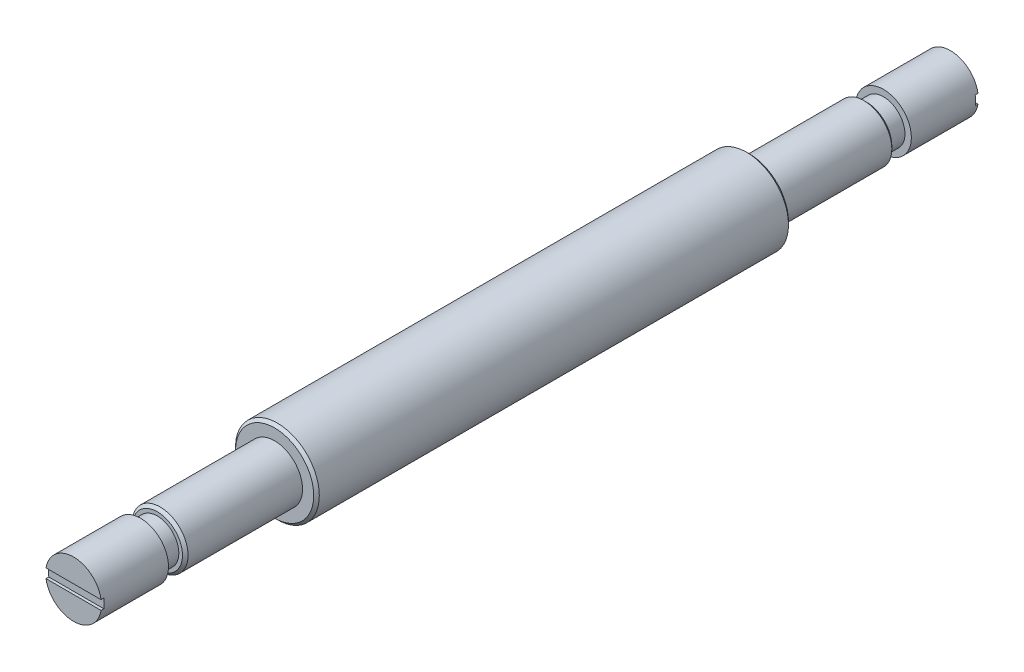
SolidWorks part; units mm, degrees
material "1.4301 (X5CrNi18-10)"
ref_plane "Plan de face" through (0, 0, 0) normal (0, 0, 1) x (1, 0, 0)
ref_plane "Plan de dessus" through (0, 0, 0) normal (0, 1, 0) x (1, 0, 0)
ref_plane "Plan de droite" through (0, 0, 0) normal (1, 0, 0) x (0, 0, -1)
sketch "Esquisse2" plane through (0, 0, 0) normal (1, 0, 0) x (0, 0, -1)
  line L0 (-66.5, 0) -> (-78.5, 0)
  line L1 (-42.5, 0) -> (42.5, 0)
  line L2 (0, 0) -> (0, 7.5)
  line L3 (-42.5, 7.5) -> (42.5, 7.5)
  line L4 (42.5, 0) -> (42.5, 7.5)
  line L5 (42.5, 0) -> (63.5, 0)
  line L6 (42.5, 0) -> (42.5, 5)
  line L7 (42.5, 5) -> (63.5, 5)
  line L8 (63.5, 0) -> (63.5, 5)
  line L9 (63.5, 0) -> (66.5, 0)
  line L10 (63.5, 0) -> (63.5, 3.85)
  line L11 (63.5, 3.85) -> (66.5, 3.85)
  line L12 (66.5, 0) -> (66.5, 3.85)
  line L13 (66.5, 0) -> (78.5, 0)
  line L14 (66.5, 0) -> (66.5, 5)
  line L15 (66.5, 5) -> (78.5, 5)
  line L16 (78.5, 0) -> (78.5, 5)
  line L17 (-78.5, 0) -> (-78.5, 5)
  line L18 (-66.5, 0) -> (-66.5, 5)
  line L19 (-63.5, 0) -> (-63.5, 5)
  line L20 (-66.5, 5) -> (-78.5, 5)
  line L21 (-66.5, 0) -> (-66.5, 3.85)
  line L22 (-63.5, 0) -> (-66.5, 0)
  line L23 (-63.5, 3.85) -> (-66.5, 3.85)
  line L24 (-42.5, 0) -> (-63.5, 0)
  line L25 (-42.5, 5) -> (-63.5, 5)
  line L26 (-42.5, 0) -> (-42.5, 7.5)
  dimension "D1" = 42.5
  dimension "D2" = 7.5
  dimension "D3" = 21
  dimension "D4" = 5
  dimension "D5" = 3
  dimension "D6" = 12
  dimension "D7" = 3.85
  dimension "D8" = 5
revolve "Révolution1" add sketch "Esquisse2" angle 360 about L1
chamfer "Chanfrein1" distance 0.5 angle 45 4 edges at (5, 0, 63.5) (7.5, 0, 42.5) (7.5, 0, -42.5) (5, 0, -63.5)
sketch "Esquisse4" plane through (0, 0, -78.5) normal (0, 0, -1) x (-1, 0, 0)
  line L1 (-5.8333, -0.8316) -> (5.8333, -0.8316)
  line L2 (-5.8333, -0.8316) -> (-5.8333, 0.8316)
  line L3 (-5.8333, 0.8316) -> (5.8333, 0.8316)
  line L4 (5.8333, -0.8316) -> (5.8333, 0.8316)
  line L5 (-5.8333, -0.8316) -> (5.8333, 0.8316) construction
  line L6 (-5.8333, 0.8316) -> (5.8333, -0.8316) construction
  point P0 (0, 0)
extrude "Enlèv. mat.-Extru.2" cut sketch "Esquisse4" against normal blind 0.5
mirror "Symétrie2" about plane through (0, 0, 0) normal (0, 0, 1) of "Enlèv. mat.-Extru.2"
